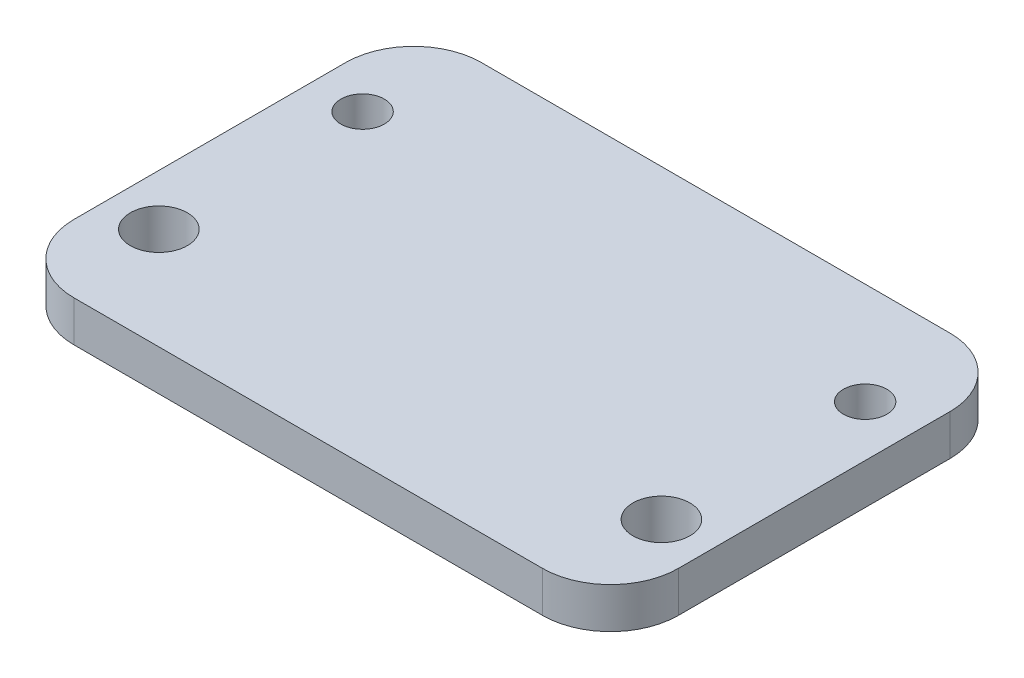
SolidWorks part; units mm, degrees
ref_plane "正面" through (0, 0, 0) normal (0, 0, 1) x (1, 0, 0)
ref_plane "平面" through (0, 0, 0) normal (0, 1, 0) x (1, 0, 0)
ref_plane "右側面" through (0, 0, 0) normal (1, 0, 0) x (0, 0, -1)
sketch "ｽｹｯﾁ1" plane through (0, 0, 0) normal (0, 1, 0) x (1, 0, 0)
  line L1 (0, 0) -> (44.5, 0)
  line L2 (0, 0) -> (0, 30)
  line L3 (0, 30) -> (44.5, 30)
  line L4 (44.5, 0) -> (44.5, 30)
  dimension "D1" = 30
  dimension "D2" = 44.5
extrude "ﾎﾞｽ - 押し出し1" add sketch "ｽｹｯﾁ1" along normal blind 3
sketch "ｽｹｯﾁ2" plane through (0, 3, 0) normal (0, 1, 0) x (1, 0, 0)
  line L0 (0, 30) -> (0, 0) construction
  line L1 (44.5, 30) -> (0, 30) construction
  line L2 (44.5, 0) -> (44.5, 30) construction
  line L3 (0, 0) -> (44.5, 0) construction
  circle A0 centre (3.75, 22.5) radius 1.6
  circle A1 centre (40.75, 22.5) radius 1.6
  circle A2 centre (3.75, 7.5) radius 2.1
  circle A3 centre (40.75, 7.5) radius 2.1
  dimension "D1" = 3.75
  dimension "D2" = 7.5
  dimension "D3" = 3.2
  dimension "D4" = 3.75
  dimension "D6" = 3.2
  dimension "D7" = 7.5
  dimension "D8" = 3.75
  dimension "D9" = 4.2
  dimension "D10" = 7.5
  dimension "D11" = 3.75
  dimension "D12" = 4.2
  dimension "D5" = 7.5
extrude "ｶｯﾄ - 押し出し1" cut sketch "ｽｹｯﾁ2" against normal blind 3
fillet "ﾌｨﾚｯﾄ1" radius 5 4 edges at (44.5, 1.5, -30) (44.5, 1.5, 0) (0, 1.5, 0) (0, 1.5, -30)
